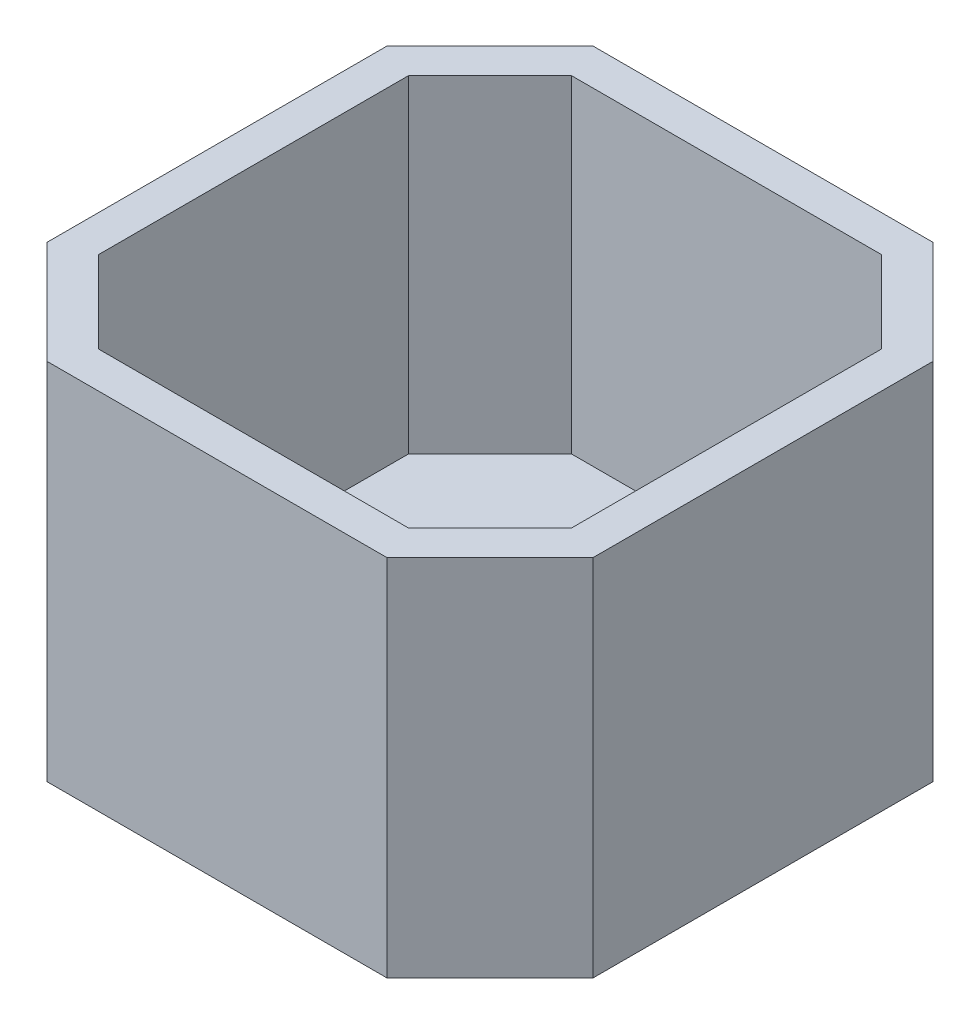
SolidWorks part; units mm, degrees
ref_plane "Front Plane" through (0, 0, 0) normal (0, 0, 1) x (1, 0, 0)
ref_plane "Top Plane" through (0, 0, 0) normal (0, 1, 0) x (1, 0, 0)
ref_plane "Right Plane" through (0, 0, 0) normal (1, 0, 0) x (0, 0, -1)
sketch "Sketch1" plane through (0, 0, 0) normal (0, 1, 0) x (1, 0, 0)
  line L0 (-9.3431, 15) -> (-15, 9.3431)
  line L1 (9.3431, -15) -> (-9.3431, -15)
  line L2 (15, -9.3431) -> (15, 9.3431)
  line L3 (9.3431, 15) -> (-9.3431, 15)
  line L4 (-15, -9.3431) -> (-15, 9.3431)
  line L5 (12.1716, -12.1716) -> (-12.1716, 12.1716) construction
  line L6 (12.1716, 12.1716) -> (-12.1716, -12.1716) construction
  line L7 (-15, -9.3431) -> (-9.3431, -15)
  line L8 (9.3431, 15) -> (15, 9.3431)
  line L9 (15, -9.3431) -> (9.3431, -15)
  line L10 (0, 15) -> (0, 0) construction
  line L11 (0, 0) -> (0, -15) construction
  line L12 (-15, 0) -> (0, 0) construction
  line L13 (0, 0) -> (15, 0) construction
  point P0 (0, 0)
  dimension "D1" = 8
  dimension "D2" = 30
extrude "Boss-Extrude1" add sketch "Sketch1" along normal blind 20
sketch "Sketch2" plane through (0, 20, 0) normal (0, 1, 0) x (1, 0, 0)
  line L0 (-9.3431, 15) -> (-15, 9.3431) construction
  line L1 (-15, 9.3431) -> (-15, -9.3431) construction
  line L2 (-15, -9.3431) -> (-9.3431, -15) construction
  line L3 (-9.3431, -15) -> (9.3431, -15) construction
  line L4 (9.3431, -15) -> (15, -9.3431) construction
  line L5 (15, -9.3431) -> (15, 9.3431) construction
  line L6 (15, 9.3431) -> (9.3431, 15) construction
  line L7 (-9.3431, 15) -> (9.3431, 15) construction
  line L9 (-8.5147, 13) -> (-13, 8.5147)
  line L10 (-13, 8.5147) -> (-13, -8.5147)
  line L11 (-13, -8.5147) -> (-8.5147, -13)
  line L12 (-8.5147, -13) -> (8.5147, -13)
  line L13 (8.5147, -13) -> (13, -8.5147)
  line L14 (13, -8.5147) -> (13, 8.5147)
  line L15 (13, 8.5147) -> (8.5147, 13)
  line L16 (-8.5147, 13) -> (8.5147, 13)
  dimension "D1" = 2
extrude "Cut-Extrude1" cut sketch "Sketch2" against normal blind 18
